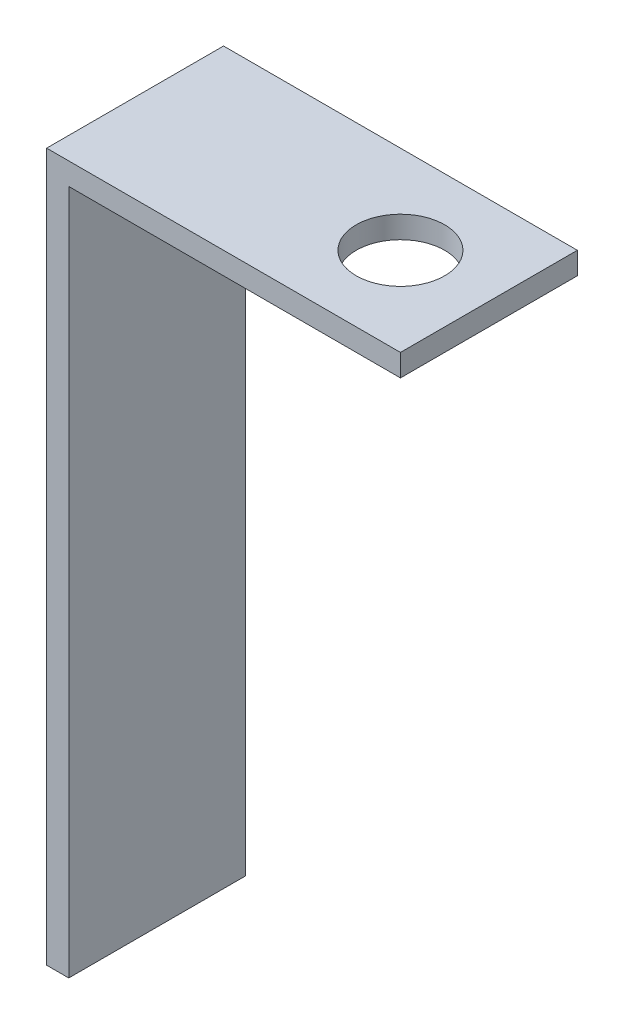
SolidWorks part; units mm, degrees
material "Plain Carbon Steel"
ref_plane "Front Plane" through (0, 0, 0) normal (0, 0, 1) x (1, 0, 0)
ref_plane "Top Plane" through (0, 0, 0) normal (0, 1, 0) x (1, 0, 0)
ref_plane "Right Plane" through (0, 0, 0) normal (1, 0, 0) x (0, 0, -1)
sketch "Sketch1" plane through (0, 0, 0) normal (0, 0, 1) x (1, 0, 0)
  line L0 (0, 0) -> (0, 50.8)
  line L1 (0, 50.8) -> (25.4, 50.8)
  dimension "D1" = 50.8
  dimension "D2" = 25.4
extrude "Extrude-Thin1" add sketch "Sketch1" along normal blind 12.7 thin
sketch "Sketch2" plane through (0, 50.8, 0) normal (0, 1, 0) x (1, 0, 0)
  line L0 (19.05, -6.35) -> (25.4, -6.35) construction
  line L1 (25.4, -12.7) -> (25.4, 0) construction
  line L2 (19.05, 0) -> (19.05, -6.35) construction
  line L3 (0, 0) -> (25.4, 0) construction
  circle A0 centre (19.05, -6.35) radius 3.175
  dimension "D1" = 6.35
extrude "Cut-Extrude1" cut sketch "Sketch2" against normal blind 10
